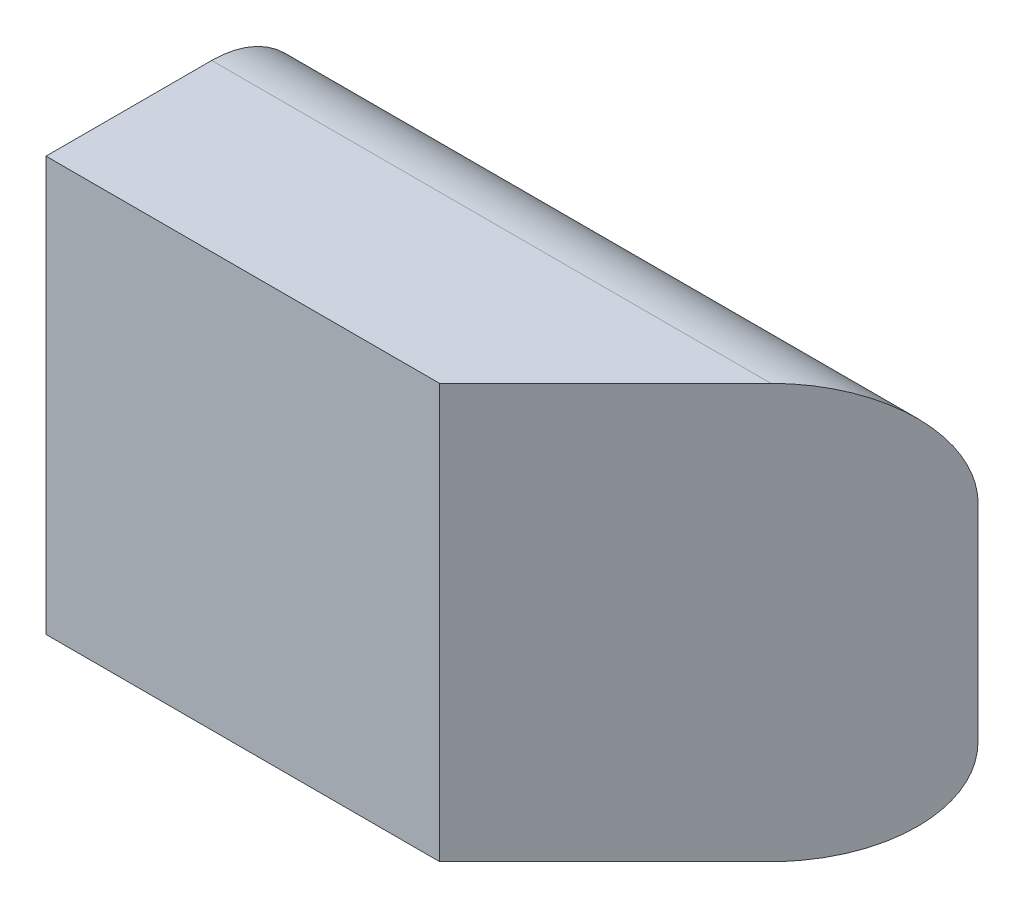
SolidWorks part; units mm, degrees
ref_plane "Front" through (0, 0, 0) normal (0, 0, 1) x (1, 0, 0)
ref_plane "Top" through (0, 0, 0) normal (0, 1, 0) x (1, 0, 0)
ref_plane "Right" through (0, 0, 0) normal (1, 0, 0) x (0, 0, -1)
sketch "Sketch1" plane through (0, 0, 0) normal (1, 0, 0) x (0, 0, -1)
  line L0 (0, 0) -> (0, 127) construction
  line L1 (0, 0) -> (31.75, 0)
  line L2 (31.75, 127) -> (0, 127)
  line L3 (63.5, 95.25) -> (63.5, 31.75)
  line L4 (0, 0) -> (-19.05, 0)
  line L5 (-19.05, 0) -> (-19.05, 127)
  line L6 (-19.05, 127) -> (0, 127)
  arc A0 (31.75, 0) -> (63.5, 31.75) centre (31.75, 31.75) ccw
  arc A1 (63.5, 95.25) -> (31.75, 127) centre (31.75, 95.25) ccw
  dimension "D2" = 63.5
  dimension "D1" = 19.05
extrude "Boss-Extrude1" add sketch "Sketch1" along normal blind 203.2
ref_plane "Mid_Plane" through (101.6, 0, 0) normal (1, 0, 0) x (0, 0, -1)
ref_plane "Plane1" through (69.85, 0, 69.85) normal (0.7071, 0, 0.7071) x (0, 1, 0)
sketch "Sketch2" plane through (69.85, 0, 69.85) normal (0.7071, 0, 0.7071) x (0, 1, 0)
  line L0 (31.75, -188.5854) -> (95.25, -188.5854) construction
  line L1 (205.1964, 201.6434) -> (-139.2061, 201.6434)
  line L2 (205.1964, 201.6434) -> (205.1964, -578.8141)
  line L3 (205.1964, -578.8141) -> (-139.2061, -578.8141)
  line L4 (-139.2061, 201.6434) -> (-139.2061, -578.8141)
  line L5 (205.1964, 201.6434) -> (-139.2061, -578.8141) construction
  line L6 (205.1964, -578.8141) -> (-139.2061, 201.6434) construction
  point P4 (32.9952, -188.5854)
extrude "Cut-Extrude1" cut sketch "Sketch2" along normal through all
